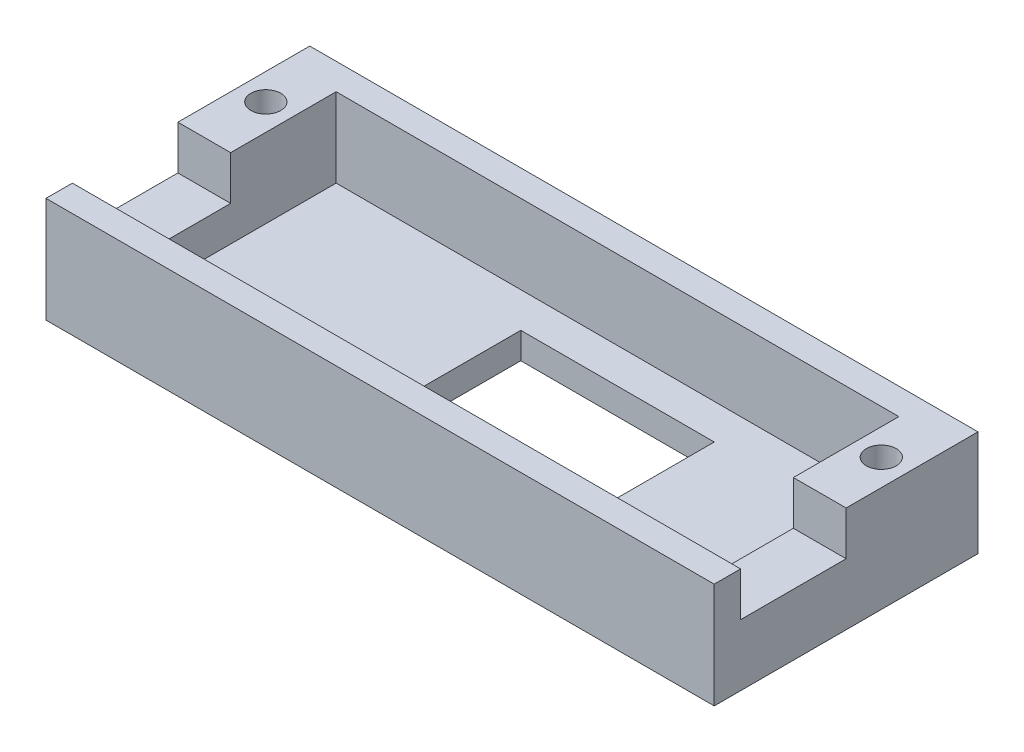
SolidWorks part; units mm, degrees
ref_plane "Front Plane" through (0, 0, 0) normal (0, 0, 1) x (1, 0, 0)
ref_plane "Top Plane" through (0, 0, 0) normal (0, 1, 0) x (1, 0, 0)
ref_plane "Right Plane" through (0, 0, 0) normal (1, 0, 0) x (0, 0, -1)
sketch "Sketch1" plane through (0, 0, 0) normal (0, 1, 0) x (1, 0, 0)
  line L1 (0, 0) -> (76, 0)
  line L2 (0, 0) -> (0, 30)
  line L3 (0, 30) -> (76, 30)
  line L4 (76, 0) -> (76, 30)
  dimension "D1" = 76
  dimension "D2" = 30
extrude "Boss-Extrude1" add sketch "Sketch1" along normal blind 12
sketch "Sketch2" plane through (0, 12, 0) normal (0, 1, 0) x (1, 0, 0)
  line L0 (0, 15) -> (76, 15) construction
  line L1 (0, 0) -> (76, 0) construction
  line L2 (0, 0) -> (0, 30) construction
  line L3 (0, 30) -> (76, 30) construction
  line L4 (76, 0) -> (76, 30) construction
  line L5 (76, 15) -> (38, 0) construction
  line L6 (38, 0) -> (38, 30) construction
  line L8 (6, 3) -> (70, 3)
  line L9 (6, 3) -> (6, 27)
  line L10 (6, 27) -> (70, 27)
  line L11 (70, 3) -> (70, 27)
  dimension "D1" = 3
  dimension "D2" = 3
  dimension "D3" = 6
  dimension "D4" = 6
extrude "Cut-Extrude1" cut sketch "Sketch2" against normal blind 9
sketch "Sketch3" plane through (0, 12, 0) normal (0, 1, 0) x (1, 0, 0)
  line L1 (76, 30) -> (0, 30) construction
  line L2 (76, 30) -> (76, 0) construction
  line L3 (76, 0) -> (0, 0) construction
  line L4 (0, 30) -> (0, 0) construction
  line L6 (73, 17) -> (73, 27) construction
  line L7 (38, 0) -> (38, 30) construction
  line L8 (70, 27) -> (76, 27) construction
  circle A0 centre (73, 22) radius 1.7
  circle A1 centre (3, 22) radius 1.7
  dimension "D1" = 3.4
  dimension "D2" = 10
  dimension "D3" = 3
extrude "Cut-Extrude2" cut sketch "Sketch3" against normal blind 20
sketch "Sketch4" plane through (0, 12, 0) normal (0, 1, 0) x (1, 0, 0)
  line L0 (76, 0) -> (76, 30) construction
  line L1 (70, 3) -> (76, 3)
  line L2 (70, 3) -> (70, 15)
  line L3 (70, 15) -> (76, 15)
  line L4 (76, 3) -> (76, 15)
  line L5 (0, 30) -> (0, 0) construction
  line L6 (6, 3) -> (0, 3)
  line L7 (6, 3) -> (6, 15)
  line L8 (6, 15) -> (0, 15)
  line L9 (0, 3) -> (0, 15)
  dimension "D1" = 12
  dimension "D2" = 12
extrude "Cut-Extrude3" cut sketch "Sketch4" against normal blind 5
sketch "Sketch5" plane through (0, 3, 0) normal (0, 1, 0) x (1, 0, 0)
  line L1 (6, 27) -> (70, 27) construction
  line L2 (6, 27) -> (6, 3) construction
  line L3 (6, 3) -> (70, 3) construction
  line L4 (70, 27) -> (70, 3) construction
  line L5 (31, 23) -> (53, 23)
  line L6 (31, 23) -> (31, 3)
  line L7 (31, 3) -> (53, 3)
  line L8 (53, 23) -> (53, 3)
  dimension "D1" = 22
  dimension "D2" = 20
  dimension "D3" = 0
  dimension "D4" = 25
extrude "Cut-Extrude4" cut sketch "Sketch5" against normal blind 5
